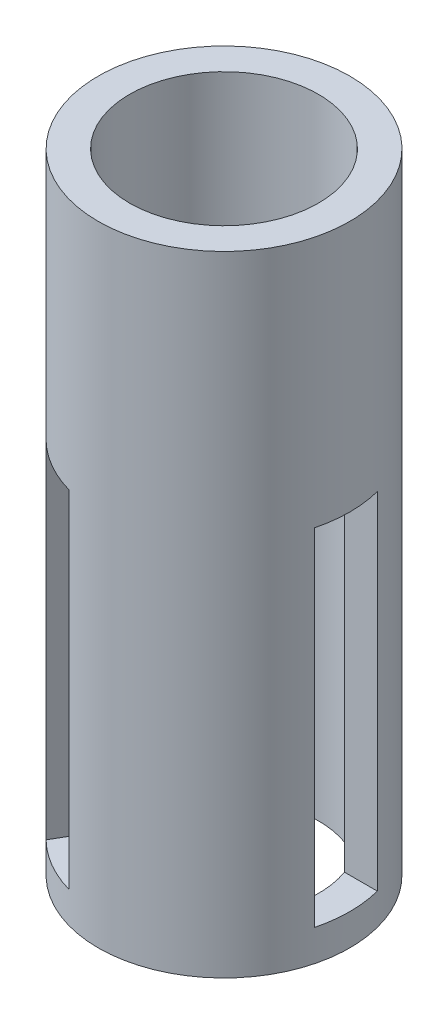
SolidWorks part; units mm, degrees
ref_plane "Front Plane" through (0, 0, 0) normal (0, 0, 1) x (1, 0, 0)
ref_plane "Top Plane" through (0, 0, 0) normal (0, 1, 0) x (1, 0, 0)
ref_plane "Right Plane" through (0, 0, 0) normal (1, 0, 0) x (0, 0, -1)
sketch "Sketch1" plane through (0, 0, 0) normal (0, 1, 0) x (1, 0, 0)
  circle A0 centre (0, 0) radius 20
  circle A1 centre (0, 0) radius 15
  dimension "D1" = 30
  dimension "D2" = 40
extrude "Boss-Extrude1" add sketch "Sketch1" along normal blind 100
ref_plane "Plane1" through (20, 0, 0) normal (1, 0, 0) x (0, 0, -1)
sketch "Sketch2" plane through (20, 0, 0) normal (1, 0, 0) x (0, 0, -1)
  line L0 (0, 73.338) -> (0, -12.5536) construction
  line L1 (5, 5) -> (-5, 5)
  line L2 (5, 5) -> (5, 60)
  line L3 (5, 60) -> (-5, 60)
  line L4 (-5, 5) -> (-5, 60)
  line L5 (5, 5) -> (-5, 60) construction
  line L6 (5, 60) -> (-5, 5) construction
  line L7 (-20, 0) -> (20, 0) construction
  point P0 (0, 32.5)
  dimension "D1" = 10
  dimension "D2" = 55
  dimension "D3" = 5
extrude "Cut-Extrude2" cut sketch "Sketch2" against normal up to surface (5.8579 mm away)
pattern_circular "CirPattern1" count 3 over 360 about axis through (0, 0, 0) along (0, 1, 0) of "Cut-Extrude2"
